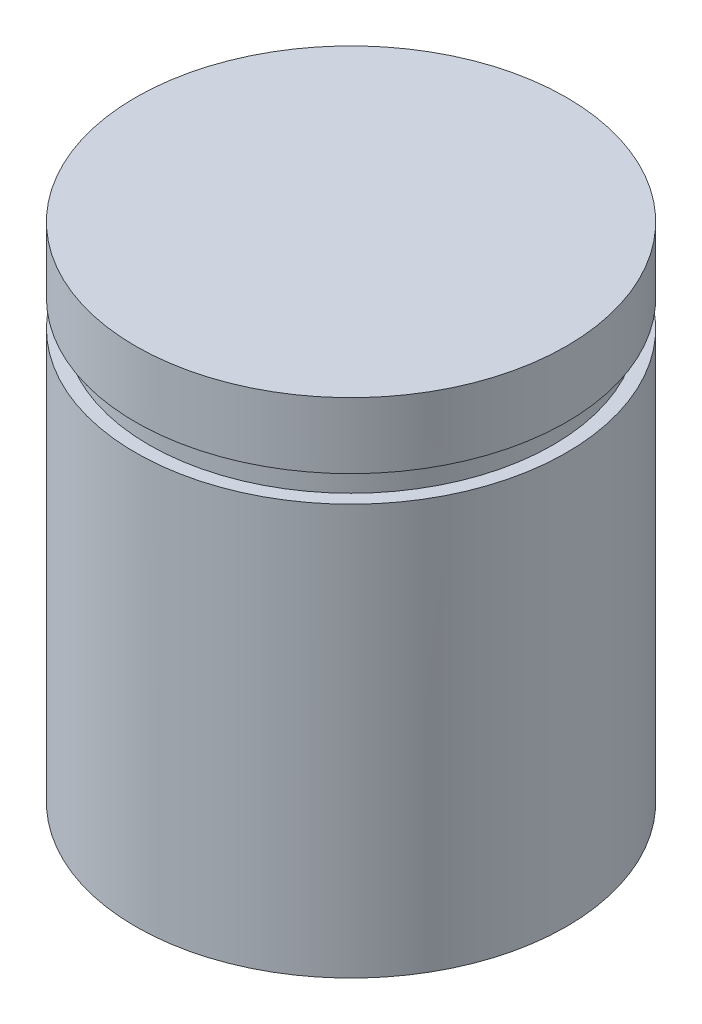
SolidWorks part; units mm, degrees
material "AISI 1020"
ref_plane "Front Plane" through (0, 0, 0) normal (0, 0, 1) x (1, 0, 0)
ref_plane "Top Plane" through (0, 0, 0) normal (0, 1, 0) x (1, 0, 0)
ref_plane "Right Plane" through (0, 0, 0) normal (1, 0, 0) x (0, 0, -1)
sketch "Sketch1" plane through (0, 0, 0) normal (0, 1, 0) x (1, 0, 0)
  circle A0 centre (0, 0) radius 6
extrude "Boss-Extrude1" add sketch "Sketch1" along normal blind 14
ref_plane "Plane1" through (0, 11.43, 0) normal (0, -1, 0) x (-1, 0, 0)
sketch "Sketch2" plane through (0, 11.43, 0) normal (0, -1, 0) x (-1, 0, 0)
  line L0 (-7.4567, 6.9858) -> (-7.4567, -7.6528)
  line L1 (-7.4567, -7.6528) -> (9.7833, -7.6528)
  line L2 (9.7833, -7.6528) -> (9.7833, 8.4993)
  line L3 (9.7833, 8.4993) -> (-7.4567, 6.9858)
  circle A0 centre (0, 0) radius 5.6261
  dimension "D1" = 11.2522
extrude "Cut-Extrude1" cut sketch "Sketch2" against normal blind 0.7366
